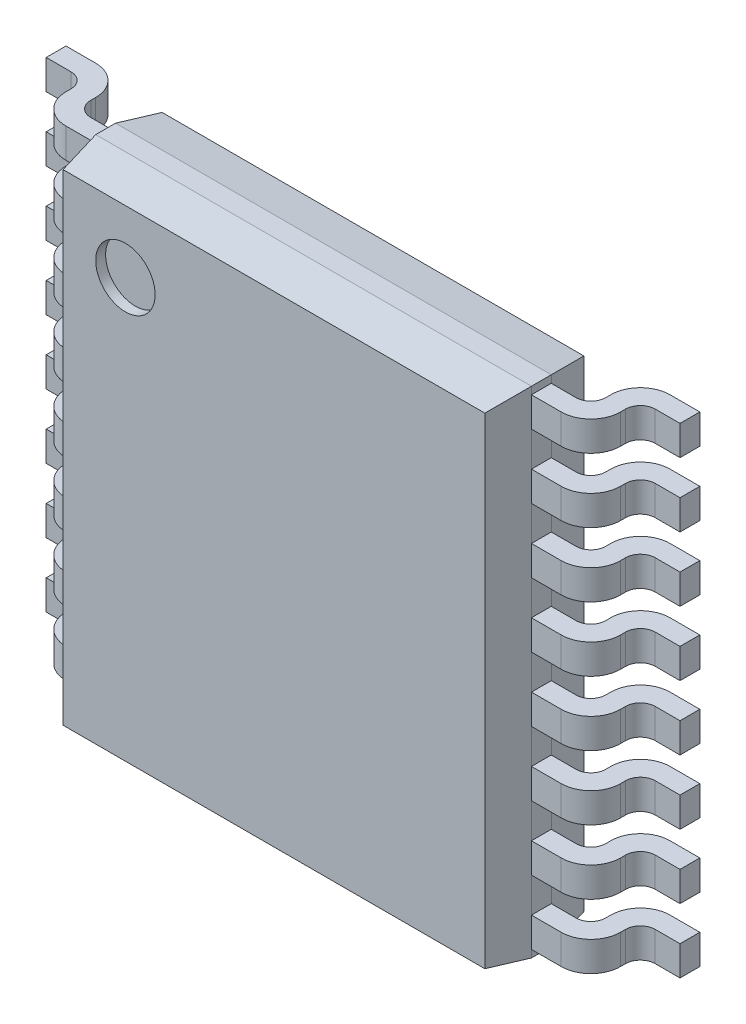
SolidWorks part; units mm, degrees
ref_plane "Спереди" through (0, 0, 0) normal (0, 0, 1) x (1, 0, 0)
ref_plane "Сверху" through (0, 0, 0) normal (0, 1, 0) x (1, 0, 0)
ref_plane "Справа" through (0, 0, 0) normal (1, 0, 0) x (0, 0, -1)
ref_plane "Плоскость1" through (0, 0, 0.1) normal (0, 0, 1) x (1, 0, 0)
sketch "Эскиз1" plane through (0, 0, 0.1) normal (0, 0, 1) x (1, 0, 0)
  line L1 (2.2, 2.5) -> (-2.2, 2.5)
  line L2 (2.2, 2.5) -> (2.2, -2.5)
  line L3 (2.2, -2.5) -> (-2.2, -2.5)
  line L4 (-2.2, 2.5) -> (-2.2, -2.5)
  line L5 (2.2, 2.5) -> (-2.2, -2.5) construction
  line L6 (2.2, -2.5) -> (-2.2, 2.5) construction
  point P0 (0, 0)
extrude "Бобышка-Вытянуть1" add sketch "Эскиз1" along normal blind 1
ref_plane "Плоскость2" through (0, 2.275, 0) normal (0, 1, 0) x (-1, 0, 0)
chamfer "Фаска1" distance 0.4 angle 10 8 edges at (0, -2.5, 0.1) (2.2, 0, 0.1) (0, 2.5, 0.1) (-2.2, 0, 0.1) (0, 2.5, 1.1) (2.2, 0, 1.1) (0, -2.5, 1.1) (-2.2, 0, 1.1)
sketch "Эскиз3" plane through (0, 2.275, 0) normal (0, 1, 0) x (-1, 0, 0)
  line L0 (0, -0.8502) -> (0, 2.6313) construction
  line L1 (-2.2, 0.6) -> (2.2, 0.6) construction
  line L2 (-2.2, 0.7) -> (-2.2, 0.5) construction
  line L3 (2.2, 0.7) -> (2.2, 0.5) construction
  line L4 (-2.2, 0.5) -> (-2.2, 0.7)
  line L5 (-2.2, 0.7) -> (-2.5, 0.7)
  line L6 (-2.2, 0.5) -> (-2.45, 0.5)
  line L7 (-2.6, 0.35) -> (-2.6, 0.3)
  line L8 (-2.9, 0) -> (-3.2, 0)
  line L9 (-3.2, 0) -> (-3.2, 0.2)
  line L10 (-3.2, 0.2) -> (-2.95, 0.2)
  line L11 (-2.8, 0.4) -> (-2.8, 0.35)
  line L12 (2.8, 0.4) -> (2.8, 0.35)
  line L13 (3.2, 0.2) -> (2.95, 0.2)
  line L14 (3.2, 0) -> (3.2, 0.2)
  line L15 (2.9, 0) -> (3.2, 0)
  line L16 (2.6, 0.35) -> (2.6, 0.3)
  line L17 (2.2, 0.5) -> (2.45, 0.5)
  line L18 (2.2, 0.7) -> (2.5, 0.7)
  line L19 (2.2, 0.5) -> (2.2, 0.7)
  arc A0 (-2.6, 0.3) -> (-2.9, 0) centre (-2.9, 0.3) cw
  arc A1 (-2.5, 0.7) -> (-2.8, 0.4) centre (-2.5, 0.4) ccw
  arc A2 (-2.45, 0.5) -> (-2.6, 0.35) centre (-2.45, 0.35) ccw
  arc A3 (-2.8, 0.35) -> (-2.95, 0.2) centre (-2.95, 0.35) cw
  arc A4 (2.8, 0.35) -> (2.95, 0.2) centre (2.95, 0.35) ccw
  arc A5 (2.45, 0.5) -> (2.6, 0.35) centre (2.45, 0.35) cw
  arc A6 (2.5, 0.7) -> (2.8, 0.4) centre (2.5, 0.4) cw
  arc A7 (2.6, 0.3) -> (2.9, 0) centre (2.9, 0.3) ccw
  dimension "D1" = 0.3
  dimension "D2" = 0.15
extrude "Бобышка-Вытянуть2" add sketch "Эскиз3" along normal blind 0.15 and the other way blind 0.15
pattern_linear "Линейный массив1" count 8 spacing 0.65 along (0, -1, 0) of "Бобышка-Вытянуть2"
sketch "Эскиз4" plane through (0, 0, 1.1) normal (0, 0, 1) x (1, 0, 0)
  circle A0 centre (-1.5, 1.8) radius 0.3
extrude "Вырез-Вытянуть1" cut sketch "Эскиз4" against normal blind 0.1
